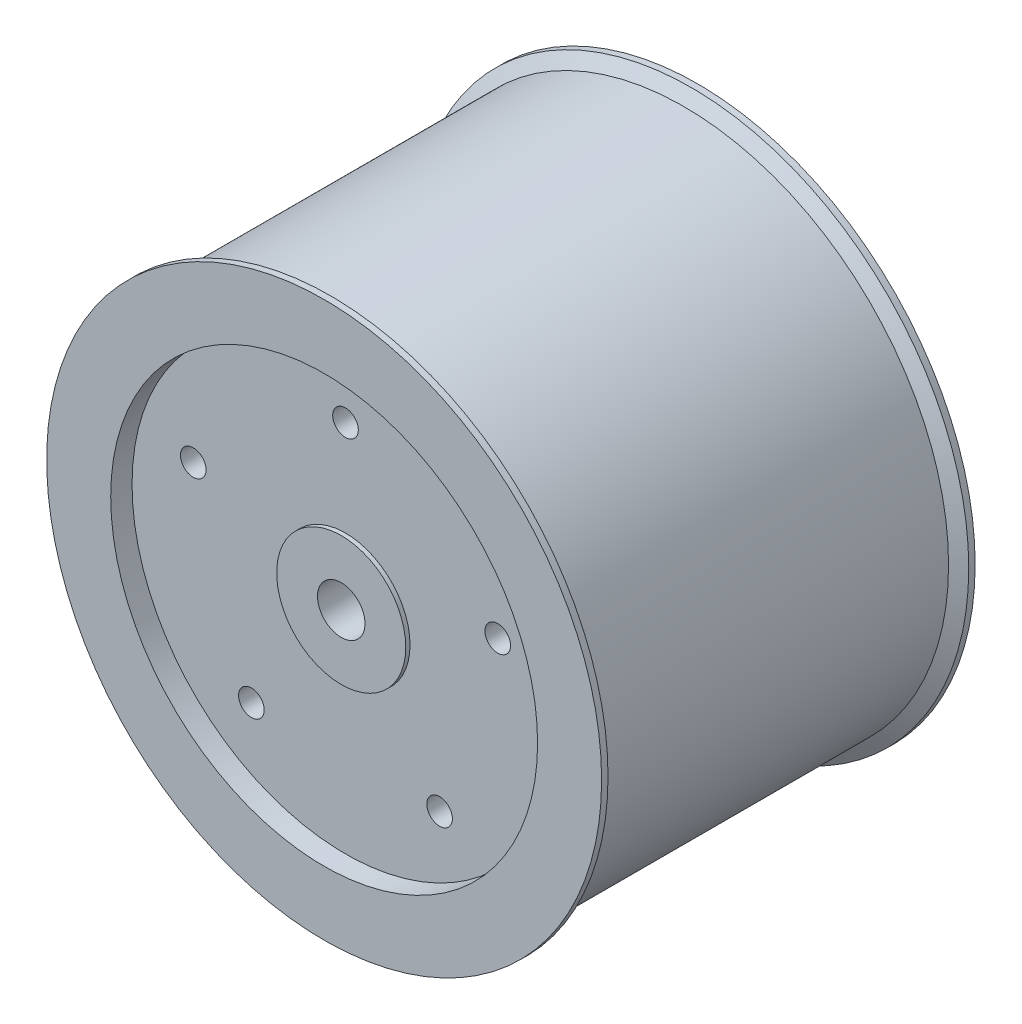
SolidWorks part; units mm, degrees
ref_plane "Front Plane" through (0, 0, 0) normal (0, 0, 1) x (1, 0, 0)
ref_plane "Top Plane" through (0, 0, 0) normal (0, 1, 0) x (1, 0, 0)
ref_plane "Right Plane" through (0, 0, 0) normal (1, 0, 0) x (0, 0, -1)
sketch "Sketch1" plane through (0, 0, 0) normal (0, 0, 1) x (1, 0, 0)
  circle A0 centre (0, 0) radius 130
  circle A1 centre (0, 0) radius 11.1125
  dimension "D1" = 260
  dimension "D2" = 22.225
extrude "Boss-Extrude1" add sketch "Sketch1" along normal mid plane 175
sketch "Sketch2" plane through (0, 0, 87.5) normal (0, 0, 1) x (1, 0, 0)
  circle A0 centre (0, 0) radius 100
  dimension "D1" = 200
extrude "Cut-Extrude1" cut sketch "Sketch2" against normal blind 10
mirror "Mirror1" about plane through (0, 0, 0) normal (0, 0, 1) of "Cut-Extrude1"
sketch "Sketch3" plane through (0, 0, 77.5) normal (0, 0, 1) x (1, 0, 0)
  circle A0 centre (0, 75) radius 6
  dimension "D1" = 12
  dimension "D2" = 75
extrude "Cut-Extrude2" cut sketch "Sketch3" against normal through all both and the other way through all
pattern_circular "CirPattern1" count 5 over 360 about axis through (0, 0, 0) along (0, 0, 1) of "Cut-Extrude2"
sketch "Sketch4" plane through (0, 0, 77.5) normal (0, 0, 1) x (1, 0, 0)
  circle A0 centre (0, 0) radius 30.2387
  circle A1 centre (0, 0) radius 11.1125 construction
  circle A2 centre (0, 0) radius 11.1125
  dimension "D1" = 60.4774
extrude "Boss-Extrude2" add sketch "Sketch4" along normal blind 2 and the other way blind 7
sketch "Sketch5" plane through (0, 0, 0) normal (0, 1, 0) x (1, 0, 0)
  line L0 (0, 0) -> (0, 34.4667) construction
  line L1 (130, 84.5) -> (124, 81.0359)
  line L2 (130, -87.5) -> (130, 87.5) construction
  line L3 (124, 81.0359) -> (124, -81.0359)
  line L4 (124, -81.0359) -> (130, -84.5)
  line L5 (130, -84.5) -> (130, 84.5)
  dimension "D1" = 3
  dimension "D2" = 3
  dimension "D3" = 6
  dimension "D4" = 120
  dimension "D5" = 60
revolve "Cut-Revolve1" cut sketch "Sketch5" angle 360 about L0
